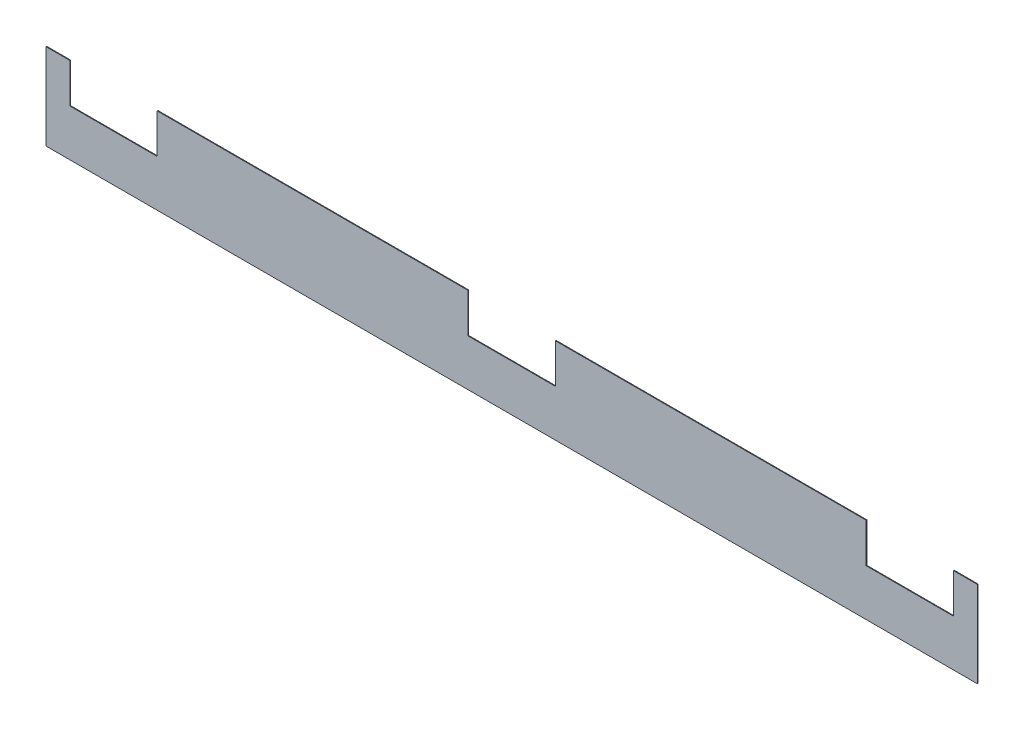
SolidWorks part; units mm, degrees
ref_plane "Plan de face" through (0, 0, 0) normal (0, 0, 1) x (1, 0, 0)
ref_plane "Plan de dessus" through (0, 0, 0) normal (0, 1, 0) x (1, 0, 0)
ref_plane "Plan de droite" through (0, 0, 0) normal (1, 0, 0) x (0, 0, -1)
sketch "Esquisse1" plane through (0, 0, 0) normal (0, 0, 1) x (1, 0, 0)
  line L0 (0, 0) -> (-3895, 0)
  line L1 (-3895, 0) -> (-3895, 360)
  line L2 (-3895, 360) -> (-3795, 360)
  line L3 (-3795, 360) -> (-3795, 195)
  line L4 (-3795, 195) -> (-3430, 195)
  line L5 (-3430, 195) -> (-3430, 360)
  line L6 (-3430, 360) -> (-2130, 360)
  line L7 (-2130, 360) -> (-2130, 195)
  line L8 (-2130, 195) -> (-1765, 195)
  line L9 (-1765, 195) -> (-1765, 360)
  line L10 (-1765, 360) -> (-465, 360)
  line L11 (-465, 360) -> (-465, 195)
  line L12 (-465, 195) -> (-100, 195)
  line L13 (-100, 195) -> (-100, 360)
  line L14 (-100, 360) -> (0, 360)
  line L15 (0, 360) -> (0, 0)
  dimension "D1" = 100
  dimension "D2" = 1300
  dimension "D3" = 365
  dimension "D4" = 365
  dimension "D5" = 365
  dimension "D6" = 1300
  dimension "D7" = 360
  dimension "D8" = 165
  dimension "D9" = 165
  dimension "D10" = 165
  dimension "D11" = 165
  dimension "D12" = 165
  dimension "D13" = 165
  dimension "D14" = 100
extrude "Boss.-Extru.1" add sketch "Esquisse1" along normal blind 3
